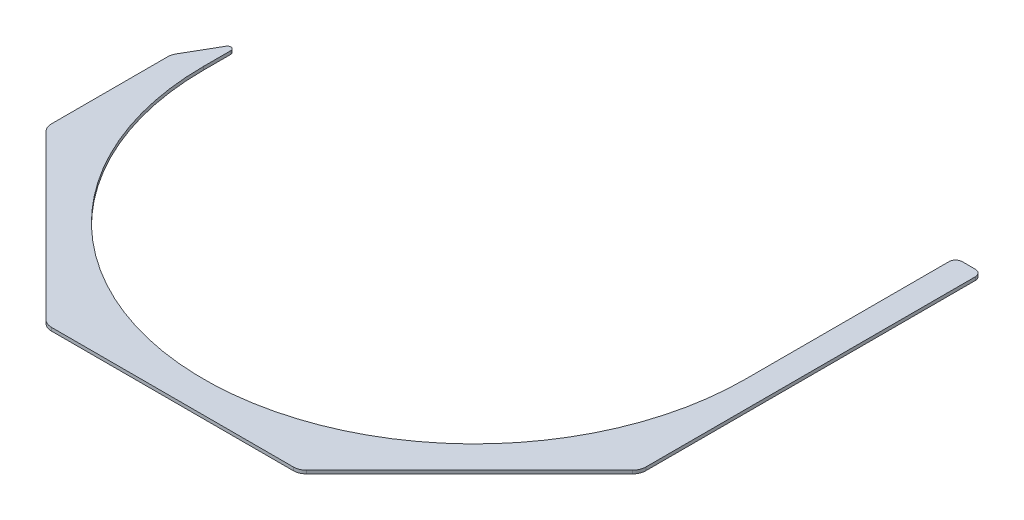
SolidWorks part; units mm, degrees
material "5052-H36"
ref_plane "Front Plane" through (0, 0, 0) normal (0, 0, 1) x (1, 0, 0)
ref_plane "Top Plane" through (0, 0, 0) normal (0, 1, 0) x (1, 0, 0)
ref_plane "Right Plane" through (0, 0, 0) normal (1, 0, 0) x (0, 0, -1)
sketch "Sketch1" plane through (0, 0, 0) normal (0, 1, 0) x (1, 0, 0)
  line L0 (-287.3375, -5.8941) -> (-287.3375, -292.1)
  line L1 (-287.3375, -5.8941) -> (-261.9375, 38.1)
  line L2 (287.3375, -292.1) -> (-287.3375, -292.1)
  line L3 (0, 0) -> (0, 15.889) construction
  line L4 (287.3375, -292.1) -> (287.3375, 203.2)
  line L5 (287.3375, 203.2) -> (261.9375, 203.2)
  line L6 (261.9375, 203.2) -> (261.9375, 0)
  line L7 (-261.9375, 0) -> (-261.9375, 38.1)
  arc A0 (-261.9375, 0) -> (261.9375, 0) centre (0, 0) ccw
  arc A1 (-261.9375, 0) -> (-256.3967, 53.5911) centre (0, 0) ccw construction
  point P4 (0, -261.9375)
  dimension "D1" = 523.875
  dimension "D4" = 495.3
  dimension "D2" = 203.2
  dimension "D3" = 38.1
  dimension "D5" = 25.4
  dimension "D6" = 30
extrude "Boss-Extrude1" add sketch "Sketch1" along normal blind 3.175
fillet "Fillet1" radius 3.175 1 edges at (-261.9375, 1.5875, -38.1)
sketch "Sketch2" plane through (0, 3.175, 0) normal (0, 1, 0) x (1, 0, 0)
  line L0 (287.3375, -292.1) -> (122.2375, -292.1)
  line L2 (122.2375, -292.1) -> (287.3375, -127)
  line L4 (287.3375, -127) -> (287.3375, -292.1)
  line L5 (-287.3375, -292.1) -> (-122.2375, -292.1)
  line L7 (-122.2375, -292.1) -> (-287.3375, -127)
  line L9 (-287.3375, -127) -> (-287.3375, -292.1)
  dimension "D2" = 165.1
extrude "Cut-Extrude1" cut sketch "Sketch2" against normal through all
fillet "Fillet2" radius 12.7 5 edges at (287.3375, 1.5875, 127) (-287.3375, 1.5875, 5.8941) (-287.3375, 1.5875, 127) (-122.2375, 1.5875, 292.1) (122.2375, 1.5875, 292.1)
fillet "Fillet3" radius 6.35 2 edges at (261.9375, 1.5875, -203.2) (287.3375, 1.5875, -203.2)
